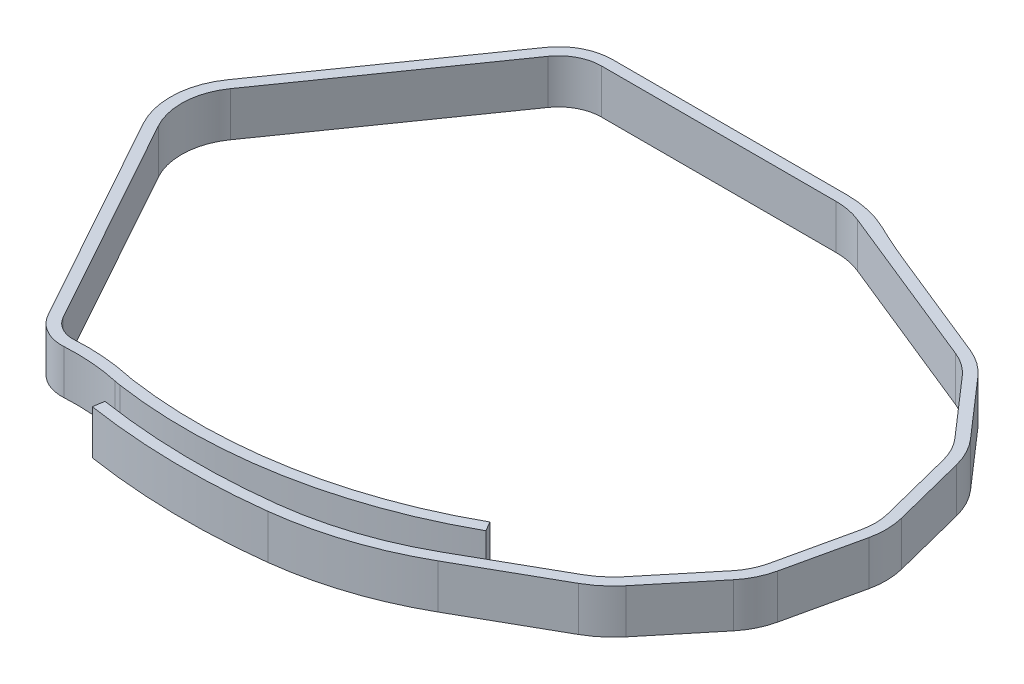
SolidWorks part; units mm, degrees
ref_plane "Front Plane" through (0, 0, 0) normal (0, 0, 1) x (1, 0, 0)
ref_plane "Top Plane" through (0, 0, 0) normal (0, 1, 0) x (1, 0, 0)
ref_plane "Right Plane" through (0, 0, 0) normal (1, 0, 0) x (0, 0, -1)
sketch "Sketch1" plane through (0, 0, 0) normal (0, 1, 0) x (1, 0, 0)
  line L25 (0, 0) -> (32, 0) construction
  line L26 (0, 0) -> (0, 5.1) construction
  line L27 (0, 5.1) -> (-11.3568, -11.1192) construction
  line L28 (-11.5142, -14.1151) -> (-1.1434, -32.8343) construction
  line L29 (32, 0) -> (32, 5.1) construction
  line L30 (32, 5.1) -> (38.396, 2.5112) construction
  line L31 (40.3662, 1.1076) -> (44.9025, -4.0916) construction
  line L32 (46.0261, -6.234) -> (47.7239, -12.9219) construction
  line L33 (47.7583, -15.3407) -> (46.2512, -22.0741) construction
  line L34 (45.189, -24.2476) -> (40.8023, -29.5737) construction
  line L35 (38.8101, -31.2464) -> (30.7168, -35.8276) construction
  line L36 (45.189, -24.2476) -> (46.2512, -22.0741) construction
  line L37 (47.7583, -15.3407) -> (47.7239, -12.9219) construction
  line L38 (46.0261, -6.234) -> (44.9025, -4.0916) construction
  line L39 (40.3662, 1.1076) -> (38.396, 2.5112) construction
  line L40 (19.7458, -40.6767) -> (19.6254, -39.6839) construction
  line L41 (32.075, 5.2854) -> (23.5423, 8.739)
  line L42 (3.7958, -39.4358) -> (3.6443, -40.4243)
  line L43 (-3.1713, 7.5491) -> (-14.9913, -9.3316)
  line L44 (-3.9904, 8.1227) -> (-15.8104, -8.758)
  line L45 (-16.1904, -15.992) -> (-5.5171, -35.2573)
  line L46 (2.8423, -39.0787) -> (2.5054, -41.0501) construction
  line L47 (32.2441, -32.2796) -> (31.228, -30.5569) construction
  line L48 (-1.1434, -32.8343) -> (-4.6424, -34.7727) construction
  line L49 (-4.6424, -34.7727) -> (-15.3156, -15.5074)
  line L50 (-4.6424, -34.7727) -> (-2.8929, -33.8035) construction
  line L51 (2, 2) -> (2, 11.4432) construction
  line L52 (2, 2) -> (30, 2) construction
  line L53 (30, 2) -> (30, 8.0671) construction
  line L54 (-13.2636, -15.0843) -> (-2.8929, -33.8035) construction
  line L55 (2, 11.4432) -> (-12.9951, -9.9721) construction
  line L59 (21.1747, 9.2) -> (0, 9.2)
  line L60 (28.6783, 7.739) -> (38.8462, 3.6236)
  line L61 (41.2705, 1.8965) -> (45.8067, -3.3027)
  line L62 (47.1892, -5.9387) -> (48.887, -12.6266)
  line L63 (48.9293, -15.6028) -> (47.4223, -22.3362)
  line L64 (46.1153, -25.0105) -> (41.7286, -30.3366)
  line L65 (39.4012, -32.2907) -> (31.3079, -36.872)
  line L67 (32.4502, 6.2123) -> (38.8462, 3.6236) construction
  line L70 (0, 10.2) -> (21.1651, 10.2)
  line L71 (-2.8929, -33.8035) -> (-1.1434, -32.8343) construction
  line L72 (3.1607, -37.9898) -> (3.45, -36.0108) construction
  line L73 (19.8422, -41.4708) -> (19.6013, -39.4854) construction
  line L74 (31.702, -37.5682) -> (30.7168, -35.8276) construction
  line L75 (31.702, -37.5682) -> (31.3079, -36.872) construction
  line L76 (-2.8929, -33.8035) -> (-1.1434, -32.8343) construction
  line L77 (31.1027, -32.3585) -> (30.6148, -31.4856)
  line L78 (32.075, 5.2854) -> (38.471, 2.6966)
  line L79 (40.5169, 1.2391) -> (45.0532, -3.9601)
  line L80 (46.2199, -6.1848) -> (47.9177, -12.8726)
  line L81 (47.9534, -15.3844) -> (46.4464, -22.1178)
  line L82 (45.3434, -24.3747) -> (40.9567, -29.7008)
  line L83 (38.9086, -31.4205) -> (30.8153, -36.0017)
  line L84 (30, 8.0671) -> (39.1463, 4.3651) construction
  line L85 (41.8733, 2.4225) -> (46.4096, -2.7768) construction
  line L86 (47.9646, -5.7419) -> (49.6624, -12.4297) construction
  line L87 (49.71, -15.7775) -> (48.2029, -22.511) construction
  line L88 (46.7328, -25.5191) -> (42.3461, -30.8452) construction
  line L89 (39.7953, -32.9869) -> (31.702, -37.5682) construction
  arc A0 (-11.3568, -11.1192) -> (-11.5142, -14.1151) centre (-9.0377, -12.7431) ccw construction
  arc A1 (-1.1434, -32.8343) -> (3.45, -36.0108) centre (4.3601, -29.7852) ccw construction
  arc A2 (38.396, 2.5112) -> (40.3662, 1.1076) centre (36.4421, -2.3162) cw construction
  arc A3 (44.9025, -4.0916) -> (46.0261, -6.234) centre (40.9783, -7.5154) cw construction
  arc A4 (47.7239, -12.9219) -> (47.7583, -15.3407) centre (42.6761, -14.2033) cw construction
  arc A5 (46.2512, -22.0741) -> (45.189, -24.2476) centre (41.1691, -20.9367) cw construction
  arc A6 (40.8023, -29.5737) -> (38.8101, -31.2464) centre (35.2962, -25.0387) cw construction
  arc A7 (30.7168, -35.8276) -> (19.6013, -39.4854) centre (16.0041, -9.8357) cw construction
  arc A8 (3.45, -36.0108) -> (31.228, -30.5569) centre (9.6063, 6.1007) ccw construction
  arc A9 (19.6013, -39.4854) -> (2.8423, -39.0787) centre (12.6143, 18.1035) cw construction
  arc A10 (19.8422, -41.4708) -> (2.5054, -41.0501) centre (12.6143, 18.1035) cw construction
  arc A11 (31.702, -37.5682) -> (19.8422, -41.4708) centre (16.0041, -9.8357) cw construction
  arc A12 (31.3079, -36.872) -> (19.7458, -40.6767) centre (16.0041, -9.8357) cw
  arc A13 (19.7458, -40.6767) -> (3.6443, -40.4243) centre (12.6143, 18.1035) cw
  arc A14 (19.6254, -39.6839) -> (2.8086, -39.2759) centre (12.6143, 18.1035) cw construction
  arc A15 (21.1747, 9.2) -> (23.5423, 8.739) centre (21.1747, 2.8893) cw
  arc A16 (-15.3156, -15.5074) -> (-14.9913, -9.3316) centre (-10.2105, -12.6791) cw
  arc A18 (-2.8929, -33.8035) -> (3.1607, -37.9898) centre (4.3601, -29.7852) ccw construction
  arc A19 (3.1607, -37.9898) -> (32.2441, -32.2796) centre (9.6063, 6.1007) ccw construction
  arc A20 (-12.9951, -9.9721) -> (-13.2636, -15.0843) centre (-9.0377, -12.7431) ccw construction
  arc A21 (-3.1713, 7.5491) -> (0, 9.2) centre (0, 5.3286) cw
  arc A22 (38.8462, 3.6236) -> (41.2705, 1.8965) centre (36.4421, -2.3162) cw
  arc A23 (45.8067, -3.3027) -> (47.1892, -5.9387) centre (40.9783, -7.5154) cw
  arc A24 (48.887, -12.6266) -> (48.9293, -15.6028) centre (42.6761, -14.2033) cw
  arc A25 (47.4223, -22.3362) -> (46.1153, -25.0105) centre (41.1691, -20.9367) cw
  arc A26 (41.7286, -30.3366) -> (39.4012, -32.2907) centre (35.2962, -25.0387) cw
  arc A27 (21.1747, 9.2) -> (28.6783, 7.739) centre (21.1747, -10.8) cw construction
  arc A28 (19.8422, -41.4708) -> (29.4052, -38.748) centre (16.0041, -9.8357) ccw construction
  arc A29 (0, 10.2) -> (-3.9904, 8.1227) centre (0, 5.3286) ccw
  arc A30 (28.6783, 7.739) -> (25.2622, 9.2578) centre (49.4645, 59.0944) cw
  arc A31 (25.2622, 9.2578) -> (21.1651, 10.2) centre (21.1651, 0.821) ccw
  arc A32 (-16.1904, -15.992) -> (-15.8104, -8.758) centre (-10.2105, -12.6791) cw
  arc A33 (3.3054, -37.0003) -> (-2.0182, -33.3189) centre (4.3601, -29.7852) cw construction
  arc A34 (-5.5171, -35.2573) -> (-2.3457, -37.0003) centre (-2.5486, -33.6128) ccw
  arc A47 (3.3054, -37.0003) -> (31.736, -31.4182) centre (9.6063, 6.1007) ccw construction
  arc A48 (-4.6424, -34.7727) -> (-2.4055, -36.0021) centre (-2.5486, -33.6128) ccw
  arc A50 (19.7361, -40.5961) -> (31.3079, -36.872) centre (16.5083, -10.7266) ccw construction
  arc A51 (3.3054, -37.0003) -> (-2.0182, -33.3189) centre (4.3601, -29.7852) cw construction
  arc A52 (3.233, -37.495) -> (2.6867, -37.3951) centre (4.3601, -29.7852) cw
  arc A53 (3.233, -37.495) -> (31.1027, -32.3585) centre (9.6063, 6.1007) ccw
  arc A54 (3.3777, -36.5055) -> (30.6148, -31.4856) centre (9.6063, 6.1007) ccw
  arc A55 (3.3777, -36.5055) -> (2.9015, -36.4185) centre (4.3601, -29.7852) cw
  arc A56 (-2.3457, -37.0003) -> (2.6867, -37.3951) centre (-1.2495, -55.2953) cw
  arc A57 (-2.4055, -36.0021) -> (2.9015, -36.4185) centre (-1.2495, -55.2953) cw
  arc A58 (3.3777, -36.5055) -> (-1.5808, -33.0766) centre (4.3601, -29.7852) cw construction
  arc A59 (3.233, -37.495) -> (-2.4555, -33.5612) centre (4.3601, -29.7852) cw construction
  arc A60 (3.3777, -36.5055) -> (31.482, -30.9876) centre (9.6063, 6.1007) ccw construction
  arc A61 (3.233, -37.495) -> (31.9901, -31.8489) centre (9.6063, 6.1007) ccw construction
  arc A62 (38.471, 2.6966) -> (40.5169, 1.2391) centre (36.4421, -2.3162) cw
  arc A63 (45.0532, -3.9601) -> (46.2199, -6.1848) centre (40.9783, -7.5154) cw
  arc A64 (47.9177, -12.8726) -> (47.9534, -15.3844) centre (42.6761, -14.2033) cw
  arc A65 (46.4464, -22.1178) -> (45.3434, -24.3747) centre (41.1691, -20.9367) cw
  arc A66 (40.9567, -29.7008) -> (38.9086, -31.4205) centre (35.2962, -25.0387) cw
  arc A67 (30.8153, -36.0017) -> (19.6254, -39.6839) centre (16.0041, -9.8357) cw
  arc A68 (19.6254, -39.6839) -> (3.7958, -39.4358) centre (12.6143, 18.1035) cw
  arc A69 (39.1463, 4.3651) -> (41.8733, 2.4225) centre (36.4421, -2.3162) cw construction
  arc A70 (46.4096, -2.7768) -> (47.9646, -5.7419) centre (40.9783, -7.5154) cw construction
  arc A71 (49.6624, -12.4297) -> (49.71, -15.7775) centre (42.6761, -14.2033) cw construction
  arc A72 (48.2029, -22.511) -> (46.7328, -25.5191) centre (41.1691, -20.9367) cw construction
  arc A73 (42.3461, -30.8452) -> (39.7953, -32.9869) centre (35.2962, -25.0387) cw construction
  point P102 (0, 0)
  point P104 (-3.6371, -34.2158)
  point P108 (2.1696, -37.2627)
  point P109 (-2.4055, -37.0003)
  dimension "D8" = 6.9
  dimension "D16" = 20
  dimension "D1" = 5.1
  dimension "D2" = 32
  dimension "D3" = 19.8
  dimension "D4" = 1
  dimension "D5" = 3
  dimension "D6" = 6.9
  dimension "D7" = 9.3
  dimension "D9" = 2
  dimension "D10" = 4
  dimension "D13" = 67.964
  dimension "D14" = 9.2
  dimension "D23" = 1
  dimension "D25" = 1
  dimension "D26" = 1
  dimension "D15" = 1.2
  dimension "D21" = 0.5
  dimension "D22" = 1
  dimension "D24" = 0.2
extrude "Boss-Extrude1" add sketch "Sketch1" along normal blind 4 contours A67 A68 L42 A13 A12 L65 A26 L64 A25 L63 A24 L62 A23 L61 A22 L60 A30 A31 L70 A29 L44 A32 L45 A34 A56 A52 A53 L77 A54 A55 A57 A48 L49 A16 L43 A21 L59 A15 L41 L78 A62 L79 A63 L80 A64 L81 A65 L82 A66 L83
